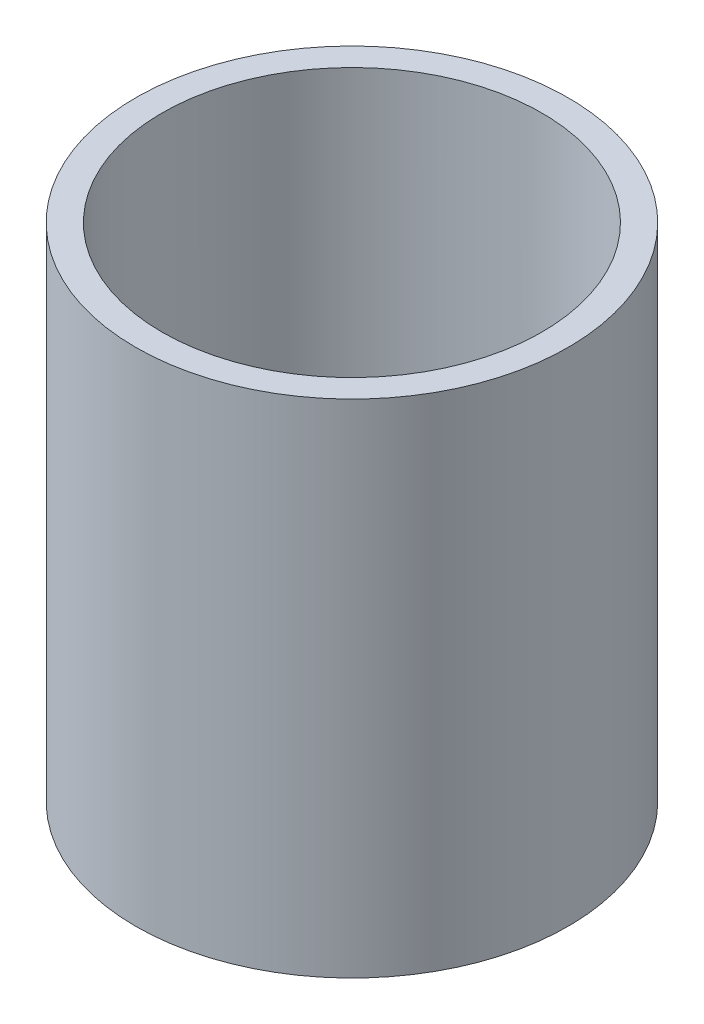
SolidWorks part; units mm, degrees
ref_plane "Front Plane" through (0, 0, 0) normal (0, 0, 1) x (1, 0, 0)
ref_plane "Top Plane" through (0, 0, 0) normal (0, 1, 0) x (1, 0, 0)
ref_plane "Right Plane" through (0, 0, 0) normal (1, 0, 0) x (0, 0, -1)
sketch "Sketch1" plane through (0, 0, 0) normal (0, 1, 0) x (1, 0, 0)
  circle A0 centre (0, 0) radius 37.95
  dimension "D1" = 75.9
extrude "Boss-Extrude1" add sketch "Sketch1" along normal blind 8
sketch "Sketch2" plane through (0, 8, 0) normal (0, 1, 0) x (1, 0, 0)
  line L0 (0, 0) -> (0, 37.95) construction
  circle A0 centre (0, 0) radius 37.95 construction
  circle A1 centre (0, 29.95) radius 1.7
  circle A2 centre (29.95, 0) radius 1.7
  circle A3 centre (0, -29.95) radius 1.7
  circle A4 centre (-29.95, 0) radius 1.7
  point P5 (-44.3724, 0.4306)
  point P8 (0, 0)
  point P16 (0, 0)
  dimension "D1" = 8
  dimension "D2" = 3.4
  dimension "D3" = 4
extrude "Cut-Extrude1" cut sketch "Sketch2" against normal through all
sketch "Sketch3" plane through (0, 8, 0) normal (0, 1, 0) x (1, 0, 0)
  line L0 (26.5725, 0) -> (28.2613, -2.925)
  line L1 (0, 26.5725) -> (2.925, 28.2613)
  line L2 (2.925, 28.2613) -> (2.925, 31.6387)
  line L3 (2.925, 31.6387) -> (0, 33.3275)
  line L4 (0, 33.3275) -> (-2.925, 31.6387)
  line L5 (-2.925, 31.6387) -> (-2.925, 28.2613)
  line L6 (-2.925, 28.2613) -> (0, 26.5725)
  line L7 (28.2613, -2.925) -> (31.6387, -2.925)
  line L8 (31.6387, -2.925) -> (33.3275, 0)
  line L9 (33.3275, 0) -> (31.6387, 2.925)
  line L10 (31.6387, 2.925) -> (28.2613, 2.925)
  line L11 (28.2613, 2.925) -> (26.5725, 0)
  line L12 (0, -26.5725) -> (-2.925, -28.2613)
  line L13 (-2.925, -28.2613) -> (-2.925, -31.6387)
  line L14 (-2.925, -31.6387) -> (0, -33.3275)
  line L15 (0, -33.3275) -> (2.925, -31.6387)
  line L16 (2.925, -31.6387) -> (2.925, -28.2613)
  line L17 (2.925, -28.2613) -> (0, -26.5725)
  line L18 (-26.5725, 0) -> (-28.2613, 2.925)
  line L19 (-28.2613, 2.925) -> (-31.6387, 2.925)
  line L20 (-31.6387, 2.925) -> (-33.3275, 0)
  line L21 (-33.3275, 0) -> (-31.6387, -2.925)
  line L22 (-31.6387, -2.925) -> (-28.2613, -2.925)
  line L23 (-28.2613, -2.925) -> (-26.5725, 0)
  circle A0 centre (0, 29.95) radius 2.925 construction
  point P1 (0, 0)
  point P31 (0, 0)
  dimension "D1" = 5.85
  dimension "D2" = 4
extrude "Cut-Extrude2" cut sketch "Sketch3" against normal blind 4
sketch "Sketch4" plane through (0, 8, 0) normal (0, 1, 0) x (1, 0, 0)
  circle A0 centre (0, 0) radius 33.3275
  circle A1 centre (0, 0) radius 37.95
  dimension "D1" = 4.6225
extrude "Boss-Extrude2" add sketch "Sketch4" along normal blind 80
